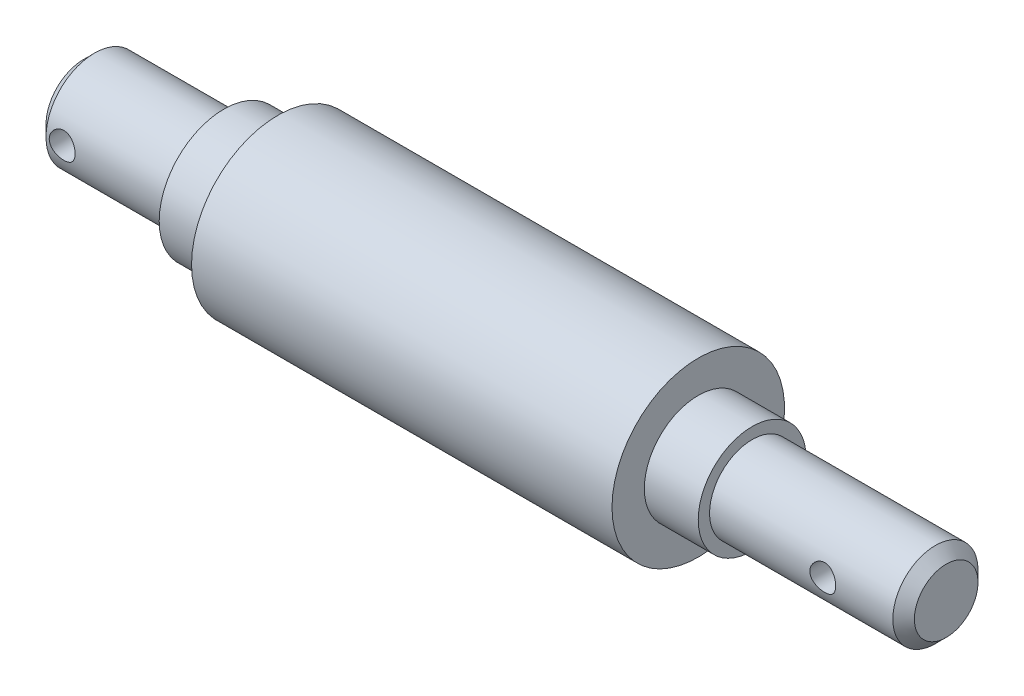
SolidWorks part; units mm, degrees
ref_plane "Front Plane" through (0, 0, 0) normal (0, 0, 1) x (1, 0, 0)
ref_plane "Top Plane" through (0, 0, 0) normal (0, 1, 0) x (1, 0, 0)
ref_plane "Right Plane" through (0, 0, 0) normal (1, 0, 0) x (0, 0, -1)
sketch "Sketch1" plane through (0, 0, 0) normal (0, 0, 1) x (1, 0, 0)
  line L0 (-41.3191, 0) -> (38.6809, 0) construction
  line L1 (-41.3191, 0) -> (-41.3191, 4.5)
  line L2 (-41.3191, 4.5) -> (-28.3335, 4.5)
  line L3 (-28.3335, 4.5) -> (-28.3191, 5.9999)
  line L4 (-28.3191, 5.9999) -> (-23.3191, 5.9999)
  line L5 (-23.3191, 5.9999) -> (-23.3191, 8)
  line L6 (-23.3191, 8) -> (15.6809, 8)
  line L7 (15.6809, 8) -> (15.6809, 5)
  line L8 (15.6809, 5) -> (20.6809, 5)
  line L9 (20.6809, 5) -> (20.6809, 3.95)
  line L10 (20.6809, 3.95) -> (38.6809, 3.95)
  line L11 (38.6809, 3.95) -> (38.6809, 0)
  line L12 (-41.3191, 0) -> (38.6809, 0)
  point P3 (0, 0)
  point P14 (0, 0)
  point P15 (0, 0)
  dimension "D1" = 80
  dimension "D2" = 18
  dimension "D3" = 5
  dimension "D4" = 5
  dimension "D5" = 18
  dimension "D6" = 3.95
  dimension "D7" = 4.5
  dimension "D8" = 8
  dimension "D9" = 5
  dimension "D10" = 1.5
revolve "Revolve1" add sketch "Sketch1" angle 360 about L0
chamfer "Chamfer1" distance 1 angle 45 2 edges at (-41.3191, 0, 4.5) (38.6809, 0, 3.95)
sketch "Sketch2" plane through (0, 0, 0) normal (0, 0, 1) x (1, 0, 0)
  line L0 (-41.3191, 3.5) -> (-41.3191, -3.5) construction
  line L1 (-3.8191, 8) -> (-3.8191, -8) construction
  line L2 (15.6809, 8) -> (-23.3191, 8) construction
  line L3 (-23.3191, -8) -> (15.6809, -8) construction
  circle A0 centre (-38.8191, 0) radius 1.2
  circle A1 centre (31.1809, 0) radius 1.2
  dimension "D1" = 2.4
  dimension "D2" = 2.5
extrude "Cut-Extrude1" cut sketch "Sketch2" against normal through all both and the other way through all
